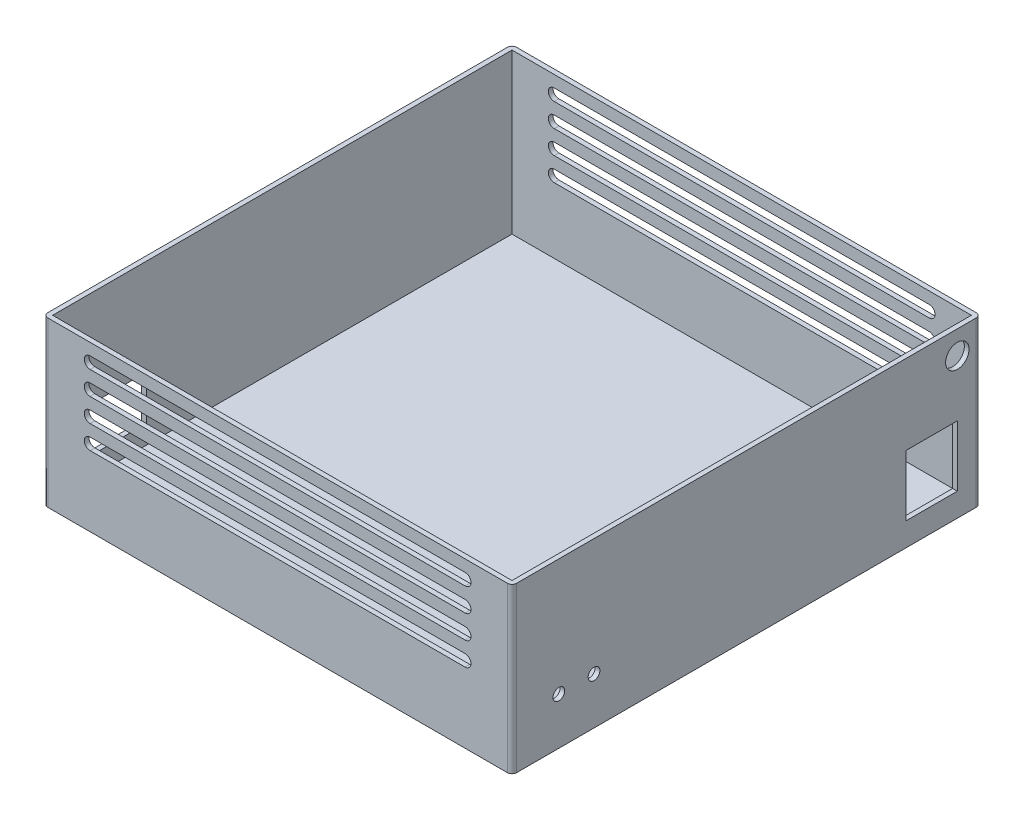
SolidWorks part; units mm, degrees
ref_plane "Front Plane" through (0, 0, 0) normal (0, 0, 1) x (1, 0, 0)
ref_plane "Top Plane" through (0, 0, 0) normal (0, 1, 0) x (1, 0, 0)
ref_plane "Right Plane" through (0, 0, 0) normal (1, 0, 0) x (0, 0, -1)
sketch "Sketch2" plane through (0, 0, 0) normal (0, 1, 0) x (1, 0, 0)
  line L1 (0, 0) -> (-200, 0)
  line L2 (0, 0) -> (0, -200)
  line L3 (0, -200) -> (-200, -200)
  line L4 (-200, 0) -> (-200, -200)
  dimension "D1" = 200
  dimension "D2" = 200
extrude "Boss-Extrude1" add sketch "Sketch2" along normal blind 70
shell "Shell2" thickness 2
sketch "Sketch3" plane through (0, 0, 200) normal (0, 0, 1) x (1, 0, 0)
  line L0 (-180, 42.5) -> (-20, 42.5) construction
  line L5 (-180, 62.5) -> (-20, 62.5) construction
  line L6 (-180, 65) -> (-20, 65)
  line L7 (-180, 60) -> (-20, 60)
  line L8 (-180, 52.5) -> (-20, 52.5) construction
  line L9 (-180, 55) -> (-20, 55)
  line L10 (-180, 50) -> (-20, 50)
  line L11 (-180, 45) -> (-20, 45)
  line L12 (-180, 40) -> (-20, 40)
  line L13 (-180, 32.5) -> (-20, 32.5) construction
  line L14 (-200, 70) -> (-200, 0) construction
  line L15 (0, 70) -> (0, 0) construction
  line L16 (-200, 70) -> (0, 70) construction
  line L17 (-180, 35) -> (-20, 35)
  line L18 (-180, 30) -> (-20, 30)
  arc A4 (-180, 65) -> (-180, 60) centre (-180, 62.5) ccw
  arc A5 (-20, 60) -> (-20, 65) centre (-20, 62.5) ccw
  arc A6 (-180, 55) -> (-180, 50) centre (-180, 52.5) ccw
  arc A7 (-20, 50) -> (-20, 55) centre (-20, 52.5) ccw
  arc A8 (-180, 45) -> (-180, 40) centre (-180, 42.5) ccw
  arc A9 (-20, 40) -> (-20, 45) centre (-20, 42.5) ccw
  arc A10 (-180, 35) -> (-180, 30) centre (-180, 32.5) ccw
  arc A11 (-20, 30) -> (-20, 35) centre (-20, 32.5) ccw
  point P7 (-100, 62.5)
  point P14 (-100, 52.5)
  point P22 (-100, 42.5)
  point P29 (-100, 32.5)
  dimension "D1" = 20
  dimension "D5" = 20
  dimension "D13" = 10
  dimension "D2" = 20
  dimension "D3" = 10
  dimension "D4" = 5
  dimension "D6" = 5
  dimension "D7" = 5
  dimension "D8" = 20
  dimension "D9" = 5
  dimension "D10" = 20
  dimension "D11" = 20
  dimension "D12" = 5
  dimension "D14" = 10
  dimension "D15" = 5
  dimension "D16" = 20
extrude "Cut-Extrude1" cut sketch "Sketch3" against normal through all both and the other way through all
sketch "Sketch5" plane through (0, 0, 0) normal (1, 0, 0) x (0, 0, -1)
  line L0 (0, 70) -> (0, 0) construction
  line L1 (-32, 36) -> (-10, 36)
  line L2 (-32, 36) -> (-32, 10)
  line L3 (-32, 10) -> (-10, 10)
  line L4 (-10, 36) -> (-10, 10)
  line L5 (-200, 0) -> (0, 0) construction
  dimension "D1" = 22
  dimension "D2" = 26
  dimension "D3" = 10
  dimension "D4" = 10
extrude "Cut-Extrude2" cut sketch "Sketch5" against normal blind 7
sketch "Sketch6" plane through (-200, 0, 0) normal (-1, 0, 0) x (0, 0, 1)
  line L0 (200, 70) -> (200, 0) construction
  line L1 (158, 29) -> (185, 29)
  line L2 (158, 29) -> (158, 10)
  line L3 (158, 10) -> (185, 10)
  line L4 (185, 29) -> (185, 10)
  line L5 (0, 0) -> (200, 0) construction
  dimension "D1" = 27
  dimension "D2" = 19
  dimension "D3" = 15
  dimension "D4" = 10
extrude "Cut-Extrude3" cut sketch "Sketch6" against normal blind 7
sketch "Sketch7" plane through (0, 0, 0) normal (1, 0, 0) x (0, 0, -1)
  line L0 (-200, 70) -> (-200, 0) construction
  line L1 (-200, 0) -> (0, 0) construction
  circle A0 centre (-180, 20) radius 2.5
  circle A1 centre (-165, 20) radius 2.5
  point P8 (0, 0)
  dimension "D1" = 5
  dimension "D2" = 5
  dimension "D3" = 15
  dimension "D4" = 20
  dimension "D5" = 20
extrude "Cut-Extrude4" cut sketch "Sketch7" against normal blind 7
sketch "Sketch8" plane through (0, 0, 0) normal (1, 0, 0) x (0, 0, -1)
  line L0 (-200, 70) -> (0, 70) construction
  line L1 (0, 70) -> (0, 0) construction
  circle A0 centre (-10, 60) radius 5
  dimension "D3" = 10
  dimension "D1" = 10
  dimension "D2" = 10
extrude "Cut-Extrude5" cut sketch "Sketch8" against normal blind 2
fillet "Fillet2" radius 2 4 edges at (0, 35, 0) (-200, 35, 200) (-200, 35, 0) (0, 35, 200)
